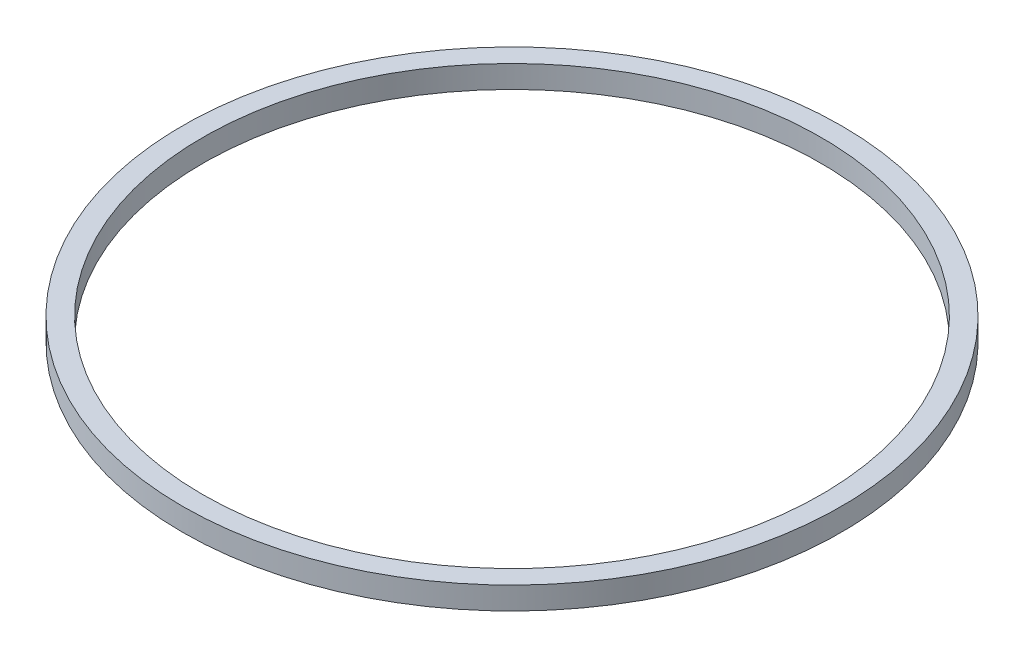
SolidWorks part; units mm, degrees
ref_plane "Front Plane" through (0, 0, 0) normal (0, 0, 1) x (1, 0, 0)
ref_plane "Top Plane" through (0, 0, 0) normal (0, 1, 0) x (1, 0, 0)
ref_plane "Right Plane" through (0, 0, 0) normal (1, 0, 0) x (0, 0, -1)
sketch "Sketch1" plane through (0, 0, 0) normal (0, 1, 0) x (1, 0, 0)
  circle A0 centre (0, 0) radius 27.5
  circle A1 centre (0, 0) radius 29.3
  dimension "D1" = 55
  dimension "D2" = 1.8
extrude "Boss-Extrude1" add sketch "Sketch1" along normal blind 2
